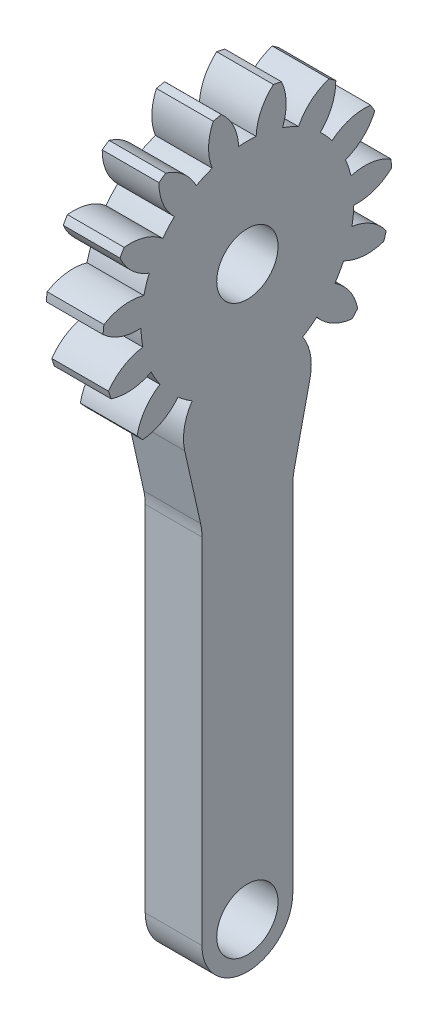
SolidWorks part; units mm, degrees
ref_plane "Plane1" through (0, 0, 0) normal (0, 0, 1) x (1, 0, 0)
ref_plane "Plane2" through (0, 0, 0) normal (0, 1, 0) x (1, 0, 0)
ref_plane "Plane3" through (0, 0, 0) normal (1, 0, 0) x (0, 0, -1)
sketch "HoldingSke" plane through (0, 0, 0) normal (0, 1, 0) x (1, 0, 0)
  line L0 (0, 0) -> (0.644, -0.1725)
  line L1 (-15, 0) -> (100, 0) construction
  line L2 (0, 0) -> (-2.1039, 2.3779)
  line L3 (0, 0) -> (-11.863, 4.5341)
  line L4 (0, 0) -> (8.3417, 2.2352)
  line L5 (0, 0) -> (-46.8476, -17.4728)
  line L6 (0, 0) -> (-4.1448, -2.7965)
  line L7 (-2.1039, 2.3779) -> (8.6596, 51.2107)
  line L8 (-76.2, 54.61) -> (-75.3, 54.61)
  line L9 (-71.009, 38.7566) -> (-53.1078, 45.2721)
  line L10 (-76.2, 71.12) -> (104.1128, 71.12)
  line L11 (0, 0) -> (-5, 0)
  line L12 (-76.2, 101.6) -> (-76.162, 101.6)
  line L13 (24.9733, 27.94) -> (52.9518, 28.4284)
  line L14 (24.9733, 27.94) -> (24.9743, 27.94)
  line L15 (24.9733, 27.94) -> (100.4006, 29.5858)
  line L16 (-63.627, -1.5) -> (-12.827, -1.5)
  circle A0 centre (0, 0) radius 2.7
  circle A1 centre (0, 0) radius 6.249
  circle A2 centre (0, 0) radius 37.5
  circle A3 centre (0, 0) radius 2.7
  dimension "MHD" = 12.498
  dimension "Hub_dia" = 75
  dimension "Bore" = 5.4
  dimension "MBD" = 5.4
  dimension "Num_teeth" = 15
  dimension "Pitch" = 0.6667
  dimension "Overall_len" = 50
  dimension "Show_teeth" = 15
  dimension "Thickness" = 5
  dimension "OAL" = 50.005
  dimension "T_dim" = 0.9
  dimension "Ap" = 20
  dimension "H" = 19.05
  dimension "Pitch_radius" = 180.3128
  dimension "Width" = 5
  dimension "Backlash" = 0.038
  dimension "Addendum_fac" = 1
  dimension "Dedendum_fac" = 1.25
  dimension "Clearance_fac" = 0.25
  dimension "Dedendum_add" = 0.001
  dimension "Module" = 1.5
sketch "BasProSke" plane through (0, 0, 0) normal (0, 1, 0) x (1, 0, 0)
  line L0 (-10, 0) -> (60, 0) construction
  line L1 (0, 0) -> (0, 12.75)
  line L2 (0, 0) -> (5, 0)
  line L3 (5, 0) -> (5, 12.75)
  line L4 (5, 12.75) -> (0, 12.75)
  dimension "Thickness" = 5
  dimension "Diameter" = 25.5
revolve "Base-Revolve" add sketch "BasProSke" angle 360 about L0
sketch "TooCutSke" plane through (0, 0, 0) normal (1, 0, 0) x (0, 0, -1)
  line L1 (0, 0) -> (0, 107) construction
  line L2 (0, 0) -> (-1.2424, 11.1812) construction
  line L3 (0, 0) -> (-4.6552, 21.901) construction
  line L4 (-1.2424, 11.1812) -> (-2.3276, 10.9505) construction
  arc A0 (0.7696, 9.3424) -> (-0.7696, 9.3424) centre (0, 0) ccw
  arc A1 (2.3153, 12.5638) -> (-2.3153, 12.5638) centre (0, 0) ccw
  circle A2 centre (0, 0) radius 11.25 construction
  circle A3 centre (0, 0) radius 10.5715 construction
  arc A4 (-0.7696, 9.3424) -> (-2.3153, 12.5638) centre (-5.2662, 9.1665) ccw
  arc A5 (2.3153, 12.5638) -> (0.7696, 9.3424) centre (5.2662, 9.1665) ccw
  dimension "Root_dia" = 18.748
  dimension "Overcut_dia" = 25.5508
  dimension "Pitch_dia" = 22.5
  dimension "Base_dia" = 21.1431
  dimension "Flank_rad" = 4.5
  dimension "Half_ang" = 12
  dimension "Half_CT" = 1.1094
extrude "ToothCut" cut sketch "TooCutSke" along normal through all
fillet "Breaks" [suppressed] radius 0.03
fillet "RootFillets" [suppressed] radius 0.376
pattern_circular "TeethCuts" count 15 every 24 about axis through (-10, 0, 0) along (1, 0, 0) of "ToothCut", "RootFillets", "Breaks"
sketch "HubNeaOneSke" plane through (0, 0, 0) normal (-1, 0, 0) x (0, 0, 1)
  circle A0 centre (0, 0) radius 6.249
  dimension "Diameter" = 12.498
extrude "HubNearOne" [suppressed] add sketch "HubNeaOneSke" along normal blind 45.005
sketch "HubNeaBotSke" plane through (0, 0, 0) normal (-1, 0, 0) x (0, 0, 1)
  circle A0 centre (0, 0) radius 6.249
  dimension "Diameter" = 12.498
extrude "HubNearBoth" [suppressed] add sketch "HubNeaBotSke" along normal blind 22.5025
ref_plane "FarPln" through (5, 0, 0) normal (1, 0, 0) x (0, 0, -1)
sketch "HubFarSke" plane through (5, 0, 0) normal (1, 0, 0) x (0, 0, -1)
  circle A0 centre (0, 0) radius 6.249
  dimension "Diameter" = 12.498
extrude "HubFar" [suppressed] add sketch "HubFarSke" along normal blind 22.5025
sketch "BorSke" plane through (0, 0, 0) normal (1, 0, 0) x (0, 0, -1)
  circle A0 centre (0, 0) radius 2.7
  dimension "Diameter" = 5.4
extrude "Bore" cut sketch "BorSke" along normal mid plane 100.01
sketch "KeySke" plane through (0, 0, 0) normal (1, 0, 0) x (0, 0, -1)
  line L0 (-1, 0) -> (-1, 3.6)
  line L1 (-1, 3.6) -> (1, 3.6)
  line L2 (1, 3.6) -> (1, 0)
  line L3 (0, 0) -> (0, 34) construction
  line L4 (-1, 0) -> (1, 0)
  dimension "Offset" = 3.6
  dimension "Width" = 2
extrude "Keyway" [suppressed] cut sketch "KeySke" along normal mid plane 100.01
pattern_circular "Keyway2" [suppressed] count 2 every 90 about axis through (-10, 0, 0) along (1, 0, 0)
sketch "Sketch3" plane through (0, 0, 0) normal (-1, 0, 0) x (0, 0, 1)
  line L0 (-5.5189, -11.4936) -> (-4, -18.2835)
  line L1 (-4, -18.2835) -> (4, -18.2835) construction
  line L2 (4, -18.2835) -> (5.5189, -11.4936)
  line L3 (-5.5189, -11.4936) -> (-2.6952, -8.9782)
  line L4 (-2.6952, -8.9782) -> (2.6952, -8.9782)
  line L5 (2.6952, -8.9782) -> (5.5189, -11.4936)
  line L6 (-4, -18.2835) -> (-4, -50)
  line L7 (-4, -50) -> (4, -50) construction
  line L8 (4, -50) -> (4, -18.2835)
  arc A0 (-4.8686, -8.0105) -> (-5.5189, -11.4936) centre (-1.1275, -10.5112) ccw construction
  arc A1 (-4, -50) -> (4, -50) centre (0, -50) ccw
  circle A2 centre (0, -50) radius 2.7
  point P13 (0, 0)
  point P20 (0, 0)
  dimension "D2" = 50
  dimension "D3" = 5.4
  dimension "D1" = 8
extrude "Boss-Extrude2" add sketch "Sketch3" against normal up to surface (5 mm away) up to face at (5, 0, 2.7)
fillet "Fillet1" radius 5 2 edges at (2.5, -18.2835, 4) (2.5, -18.2835, -4)
equation "' \"Module@HoldingSke\" = 6.35"
equation "' \"Num_teeth@HoldingSke\" = 12"
equation "' \"Ap@HoldingSke\" =  20"
equation "' \"Ap@HoldingSke\" = 20"
equation "' \"Width@HoldingSke\" = 0.5 * 25.4"
equation "' \"Hub_dia@HoldingSke\"= 1 * 25.4"
equation "' \"Hub_dia@HoldingSke\" = 1 * 25.4"
equation "' \"Overall_len@HoldingSke\" = 1.0 * 25.4"
equation "' \"Bore@HoldingSke\" = 0.75 * 25.4"
equation "' \"T_dim@HoldingSke\" = 0.1 * 25.4"
equation "' \"Width@KeySke\" = 0.25 * 25.4"
equation "' \"Show_teeth@HoldingSke\" = 13"
equation "' \"Backlash@HoldingSke\" = 0.009 * 25.4"
equation "' \"Addendum_fac@HoldingSke\" = 1.0"
equation "' \"Dedendum_fac@HoldingSke\" = 1.25"
equation "' \"Dedendum_add@HoldingSke\" = 0.00005 * 25.4"
equation "' \"Clearance_fac@HoldingSke\" = 0.25"
equation "\"Pitch@HoldingSke\" = 1 / \"Module@HoldingSke\""
equation "\"Overcut_dia@TooCutSke\" = (\"Num_teeth@HoldingSke\" + 2 * \"Addendum_fac@HoldingSke\") / \"Pitch@HoldingSke\" + 0.002 * 25.4"
equation "\"Pitch_dia@TooCutSke\" = \"Num_teeth@HoldingSke\" / \"Pitch@HoldingSke\""
equation "\"Base_dia@TooCutSke\" = \"Num_teeth@HoldingSke\" / \"Pitch@HoldingSke\" * cos((\"Ap@HoldingSke\"  * 3.14159265 / 180))"
equation "\"Root_dia@TooCutSke\" = (\"Num_teeth@HoldingSke\" + 2) / \"Pitch@HoldingSke\" - 2 * (\"Addendum_fac@HoldingSke\" + \"Dedendum_fac@HoldingSke\") / \"Pitch@HoldingSke\" - \"Dedendum_add@HoldingSke\" * 2"
equation "\"Half_ang@TooCutSke\" = 180 / \"Num_teeth@HoldingSke\""
equation "\"Half_CT@TooCutSke\" = \"Num_teeth@HoldingSke\" / \"Pitch@HoldingSke\" * sin((3.14159265 / 2 / \"Num_teeth@HoldingSke\")) / 2 - 7 * \"Backlash@HoldingSke\" / 4"
equation "\"Flank_rad@TooCutSke\" = \"Num_teeth@HoldingSke\" / \"Pitch@HoldingSke\" / 5"
equation "\"Radius@RootFillets\" = \"Clearance_fac@HoldingSke\" / \"Pitch@HoldingSke\" + \"Dedendum_add@HoldingSke\""
equation "\"Break_rad@Breaks\" = 0.02 / \"Pitch@HoldingSke\""
equation "\"Thickness@HoldingSke\" = \"Width@HoldingSke\""
equation "\"OAL@HoldingSke\" = \"Thickness@HoldingSke\""
equation "\"MHD@HoldingSke\" = (\"Num_teeth@HoldingSke\" + 2) / \"Pitch@HoldingSke\" - 2 * (\"Addendum_fac@HoldingSke\" + \"Dedendum_fac@HoldingSke\")  / \"Pitch@HoldingSke\" - \"Dedendum_add@HoldingSke\" * 2"
equation "\"MBD@HoldingSke\" = (\"Num_teeth@HoldingSke\" + 2) / \"Pitch@HoldingSke\" - 2 * (\"Addendum_fac@HoldingSke\" + \"Dedendum_fac@HoldingSke\")  / \"Pitch@HoldingSke\" - \"Dedendum_add@HoldingSke\" * 2 - 0.002 * 25.4"
equation "\"MHD@HoldingSke\" = ((sgn( \"MHD@HoldingSke\" - \"Hub_dia@HoldingSke\" )-1)*( \"MHD@HoldingSke\" - \"Hub_dia@HoldingSke\" ))/-2+ \"Hub_dia@HoldingSke\""
equation "\"MBD@HoldingSke\"=\"Bore@HoldingSke\""
equation "\"OAL@HoldingSke\" = ((sgn( \"OAL@HoldingSke\" - \"Overall_len@HoldingSke\" )+1)*( \"OAL@HoldingSke\" - \"Overall_len@HoldingSke\" ))/2 + \"Overall_len@HoldingSke\" + 0.000002 * 25.4"
equation "\"Num_teeth@TeethCuts\" = int( \"Show_teeth@HoldingSke\" ) + 1"
equation "\"Num_teeth@TeethCuts\" = ((sgn( \"Num_teeth@TeethCuts\" - \"Num_teeth@HoldingSke\" )-1)*( \"Num_teeth@TeethCuts\" - \"Num_teeth@HoldingSke\" ))/-2+ \"Num_teeth@HoldingSke\""
equation "\"Num_teeth@TeethCuts\" = ((sgn( \"Num_teeth@TeethCuts\" - 2.0)+1)*( \"Num_teeth@TeethCuts\" - 2.0))/2 +2.0"
equation "\"Angle@TeethCuts\" = 360.0 / \"Num_teeth@HoldingSke\""
equation "\"Diameter@BasProSke\" = (\"Num_teeth@HoldingSke\" + 2 * \"Addendum_fac@HoldingSke\") / \"Pitch@HoldingSke\""
equation "\"Thickness@BasProSke\"  = \"Thickness@HoldingSke\""
equation "' \"Fillet_rad@BasProSke\" =  \"Thickness@HoldingSke\" * 0.05"
equation "' \"Fillet_rad@BasProSke\" = \"Thickness@HoldingSke\" * 0.05"
equation "\"MHD@HoldingSke\" = ((sgn( \"MHD@HoldingSke\" - \"Root_dia@TooCutSke\" )-1)*( \"MHD@HoldingSke\" - \"Root_dia@TooCutSke\" ))/-2+ \"Root_dia@TooCutSke\""
equation "\"Diameter@HubNeaOneSke\" = \"MHD@HoldingSke\""
equation "\"Length@HubNearOne\" = \"OAL@HoldingSke\" - \"Thickness@BasProSke\""
equation "\"Diameter@HubNeaBotSke\" = \"MHD@HoldingSke\""
equation "\"Length@HubNearBoth\" = ( \"OAL@HoldingSke\" - \"Thickness@BasProSke\" ) / 2.0"
equation "\"Thickness@FarPln\" = \"Thickness@BasProSke\""
equation "\"Diameter@HubFarSke\" = \"MHD@HoldingSke\""
equation "\"Length@HubFar\" = ( \"OAL@HoldingSke\" - \"Thickness@BasProSke\" ) / 2.0"
equation "\"Diameter@BorSke\" = \"MBD@HoldingSke\""
equation "\"D1@Bore\" = \"OAL@HoldingSke\" * 2.0"
equation "\"D1@Keyway\" = \"OAL@HoldingSke\" * 2.0"
equation "\"Offset@KeySke\" = \"T_dim@HoldingSke\" + \"MBD@HoldingSke\" / 2.0"
